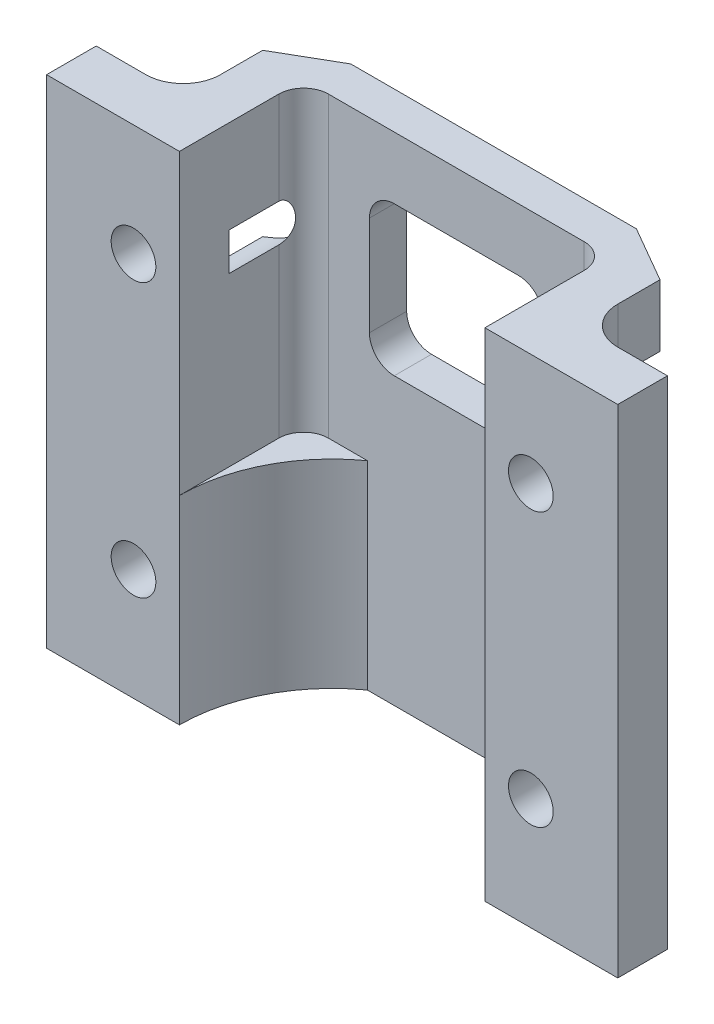
SolidWorks part; units mm, degrees
ref_plane "前视基准面" through (0, 0, 0) normal (0, 0, 1) x (1, 0, 0)
ref_plane "上视基准面" through (0, 0, 0) normal (0, 1, 0) x (1, 0, 0)
ref_plane "右视基准面" through (0, 0, 0) normal (1, 0, 0) x (0, 0, -1)
sketch "草图1" plane through (0, 0, 0) normal (0, 1, 0) x (1, 0, 0)
  line L0 (-6.15, 0) -> (-11.5, 0)
  line L1 (6.15, 0) -> (11.5, 0)
  line L2 (0, 0) -> (0, 11.3245) construction
  line L3 (-11.5, 0) -> (-11.5, 2)
  line L4 (-11.5, 2) -> (-8, 2)
  line L5 (-8, 2) -> (-8, 6.5)
  line L6 (-3.5809, 5) -> (3.5809, 5)
  line L7 (-8, 6.5) -> (8, 6.5)
  line L8 (8, 6.5) -> (8, 2)
  line L9 (8, 2) -> (11.5, 2)
  line L10 (11.5, 2) -> (11.5, 0)
  arc A0 (-3.5809, 5) -> (-6.15, 0) centre (0, 0) ccw
  arc A1 (6.15, 0) -> (3.5809, 5) centre (0, 0) ccw
  dimension "D1" = 12.3
  dimension "D2" = 23
  dimension "D3" = 5
  dimension "D4" = 2
  dimension "D5" = 3.5
  dimension "D7" = 1.5
  dimension "D8" = 16
extrude "凸台-拉伸1" add sketch "草图1" along normal blind 20
sketch "草图2" plane through (0, 20, 0) normal (0, 1, 0) x (1, 0, 0)
  line L0 (-3.5809, 5) -> (3.5809, 5) construction
  line L1 (-6.15, 0) -> (6.15, 0)
  line L2 (-6.15, 0) -> (-6.15, 5)
  line L3 (-6.15, 5) -> (6.15, 5)
  line L4 (6.15, 0) -> (6.15, 5)
extrude "切除-拉伸1" cut sketch "草图2" against normal offset from surface (12 mm away) 8 up to face at (0, 0, -2.6351)
fillet "圆角1" radius 1 2 edges at (-6.15, 14, -5) (6.15, 14, -5)
fillet "圆角2" radius 1.5 2 edges at (8, 10, -2) (-8, 10, -2)
sketch "草图6" plane through (0, 20, 0) normal (0, 1, 0) x (1, 0, 0)
  line L0 (-5.75, 6.5) -> (-8.5285, 4.8958)
  line L1 (8, 6.5) -> (-8, 6.5) construction
  line L2 (-8.5285, 4.8958) -> (-8.5285, 6.5)
  line L3 (-8.5285, 6.5) -> (-5.75, 6.5)
  line L4 (0, 8.479) -> (0, 0) construction
  line L5 (8.5285, 6.5) -> (5.75, 6.5)
  line L6 (8.5285, 4.8958) -> (8.5285, 6.5)
  line L7 (5.75, 6.5) -> (8.5285, 4.8958)
  dimension "D1" = 30
  dimension "D2" = 11.5
extrude "切除-拉伸5" cut sketch "草图6" against normal through all
sketch "草图3" plane through (0, 0, -6.5) normal (0, 0, -1) x (-1, 0, 0)
  line L0 (0, 20.7424) -> (0, 0) construction
  line L1 (-5.75, 0) -> (5.75, 0) construction
  circle A0 centre (-8, 4.5) radius 0.9
  circle A1 centre (-8, 15.5) radius 0.9
  circle A2 centre (8, 15.5) radius 0.9
  circle A3 centre (8, 4.5) radius 0.9
  dimension "D1" = 1.8
  dimension "D2" = 16
  dimension "D3" = 4.5
  dimension "D4" = 11
extrude "切除-拉伸2" cut sketch "草图3" against normal blind 8
sketch "草图4" plane through (0, 0, -2) normal (0, 0, -1) x (-1, 0, 0)
  circle A0 centre (-8, 15.5) radius 2
  circle A1 centre (-8, 4.5) radius 2
  circle A2 centre (8, 15.5) radius 2
  circle A3 centre (8, 4.5) radius 2
  dimension "D1" = 4
extrude "切除-拉伸3" cut sketch "草图4" along normal blind 8
sketch "草图5" plane through (0, 0, -5) normal (0, 0, 1) x (1, 0, 0)
  line L0 (0, 0) -> (0, 26.3521) construction
  line L1 (-2.5, 17.5) -> (2.5, 17.5)
  line L2 (-3.5, 16.5) -> (-3.5, 12.5)
  line L3 (-2.5, 11.5) -> (2.5, 11.5)
  line L4 (3.5, 16.5) -> (3.5, 12.5)
  line L5 (-5.15, 20) -> (5.15, 20) construction
  arc A0 (2.5, 11.5) -> (3.5, 12.5) centre (2.5, 12.5) ccw
  arc A1 (2.5, 17.5) -> (3.5, 16.5) centre (2.5, 16.5) cw
  arc A2 (-3.5, 12.5) -> (-2.5, 11.5) centre (-2.5, 12.5) ccw
  arc A3 (-2.5, 17.5) -> (-3.5, 16.5) centre (-2.5, 16.5) ccw
  point P13 (3.5, 17.5)
  point P16 (-3.5, 11.5)
  point P19 (-3.5, 17.5)
  dimension "D4" = 1
  dimension "D1" = 7
  dimension "D2" = 2.5
  dimension "D3" = 6
extrude "切除-拉伸4" cut sketch "草图5" against normal blind 8
